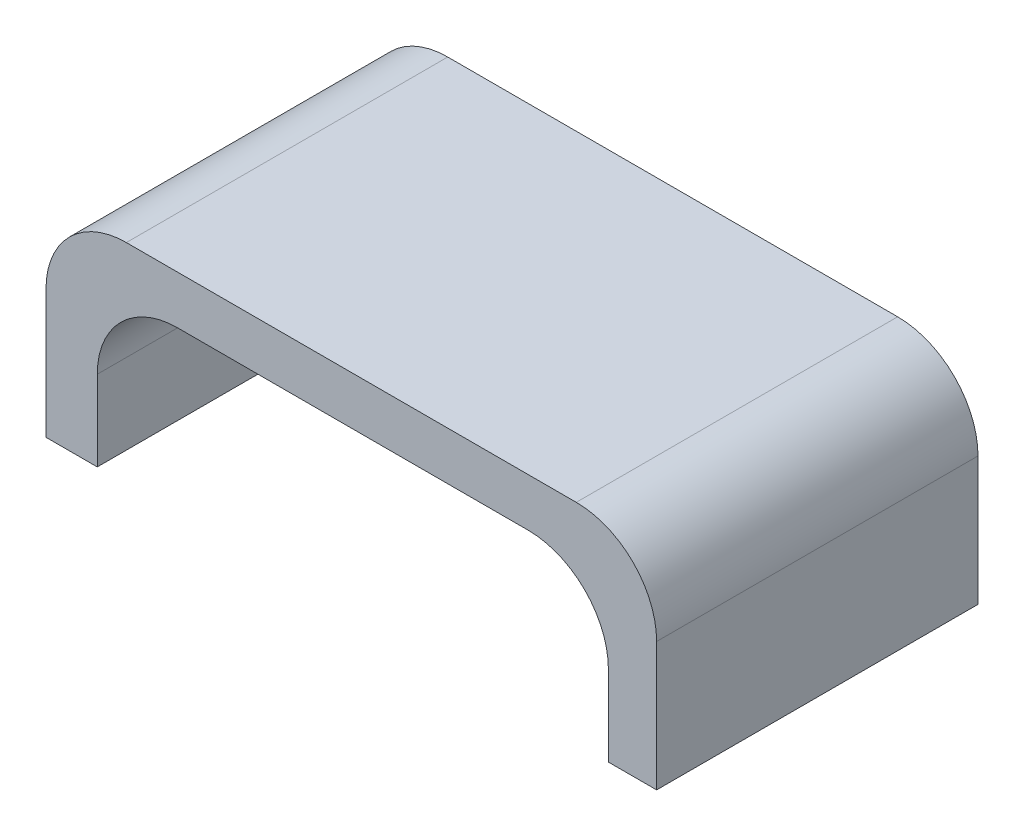
SolidWorks part; units mm, degrees
ref_plane "Front" through (0, 0, 0) normal (0, 0, 1) x (1, 0, 0)
ref_plane "Top" through (0, 0, 0) normal (0, 1, 0) x (1, 0, 0)
ref_plane "Right" through (0, 0, 0) normal (1, 0, 0) x (0, 0, -1)
sketch "草图1" plane through (0, 0, 0) normal (0, 0, 1) x (1, 0, 0)
  line L0 (0, 0) -> (0, 52.472) construction
  line L2 (-38, 14.0053) -> (-38, 20.0095)
  line L4 (38, 14) -> (38, 20)
  line L11 (38, 14) -> (32, 14)
  line L12 (28, 40) -> (-28, 40)
  line L14 (38, 20) -> (38, 30)
  line L15 (-38, 30) -> (-38, 20.0095)
  line L17 (32, 14) -> (32, 24)
  line L19 (22, 34) -> (-21.6161, 34)
  line L21 (-38, 14.0053) -> (-31.6161, 14.0053)
  line L22 (-31.6161, 14.0053) -> (-31.6161, 24)
  arc A0 (-31.6161, 24) -> (-21.6161, 34) centre (-21.6161, 24) cw
  arc A1 (22, 34) -> (32, 24) centre (22, 24) cw
  arc A2 (-28, 40) -> (-38, 30) centre (-28, 30) ccw
  arc A3 (38, 30) -> (28, 40) centre (28, 30) ccw
  point P8 (-37.9515, 14.0248)
  point P15 (-31.4891, 35.0226)
  point P23 (38, 40)
  dimension "D7" = 10
  dimension "D8" = 10
  dimension "D1" = 76
  dimension "D2" = 38
  dimension "D3" = 6
  dimension "D4" = 6
  dimension "D5" = 6
  dimension "D6" = 20
extrude "凸台-拉伸1" add sketch "草图1" along normal blind 40
